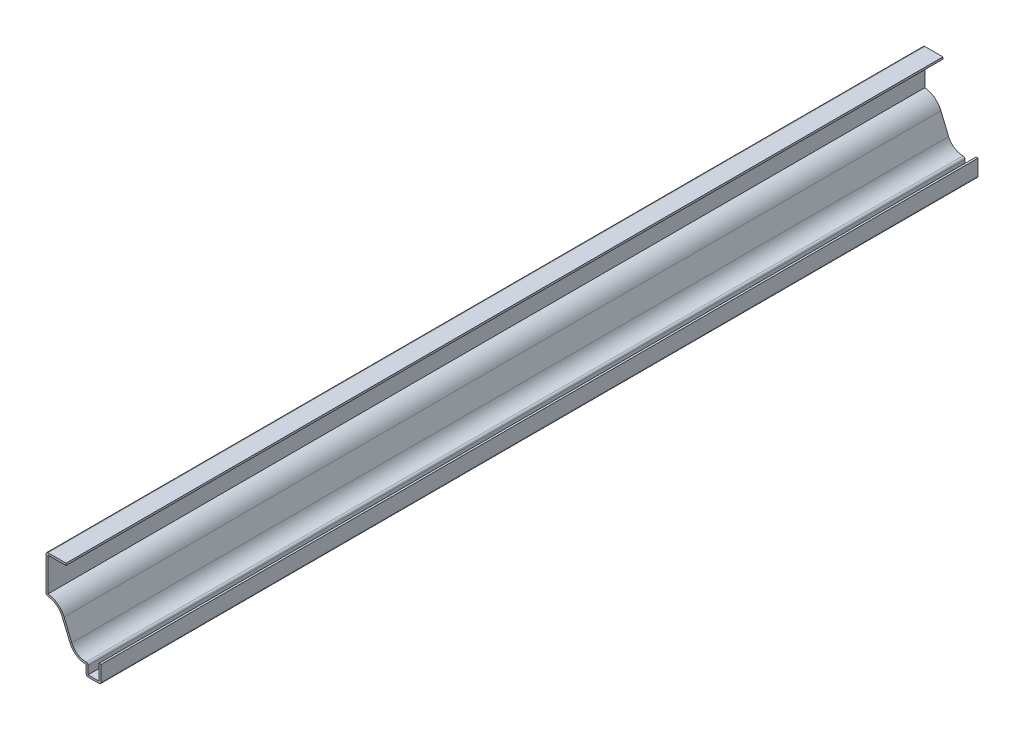
SolidWorks part; units mm, degrees
ref_plane "Front Plane" through (0, 0, 0) normal (0, 0, 1) x (1, 0, 0)
ref_plane "Top Plane" through (0, 0, 0) normal (0, 1, 0) x (1, 0, 0)
ref_plane "Right Plane" through (0, 0, 0) normal (1, 0, 0) x (0, 0, -1)
sketch "Sketch1" plane through (0, 0, 0) normal (0, 0, 1) x (1, 0, 0)
  line L0 (0, 0) -> (0, -11.1125)
  line L1 (0, -11.1125) -> (-9.525, -11.1125)
  line L2 (-9.525, -11.1125) -> (-9.525, -4.7625)
  line L3 (-19.7827, 2.076) -> (-24.6673, 13.799)
  line L4 (-34.925, 20.6375) -> (-34.925, 44.45)
  line L5 (-34.925, 44.45) -> (-22.225, 44.45)
  arc A0 (-9.525, -4.7625) -> (-19.7827, 2.076) centre (-9.525, 6.35) cw
  arc A1 (-24.6673, 13.799) -> (-34.925, 20.6375) centre (-34.925, 9.525) ccw
  point P10 (0, 0)
  point P13 (0, 0)
  dimension "D10" = 11.1125
  dimension "D11" = 11.1125
  dimension "D1" = 55.5625
  dimension "D2" = 34.925
  dimension "D3" = 11.1125
  dimension "D4" = 9.525
  dimension "D5" = 6.35
  dimension "D6" = 12.7
  dimension "D7" = 23.8125
  dimension "D8" = 25.4
  dimension "D9" = 44.45
extrude "Extrude-Thin1" add sketch "Sketch1" against normal blind 555.625 thin
fillet "Fillet1" radius 1.27 5 edges at (0, -11.1125, -277.8125) (-9.525, -11.1125, -277.8125) (-8.255, -3.4102, -277.8125) (-34.925, 20.6375, -277.8125) (-34.925, 44.45, -277.8125)
